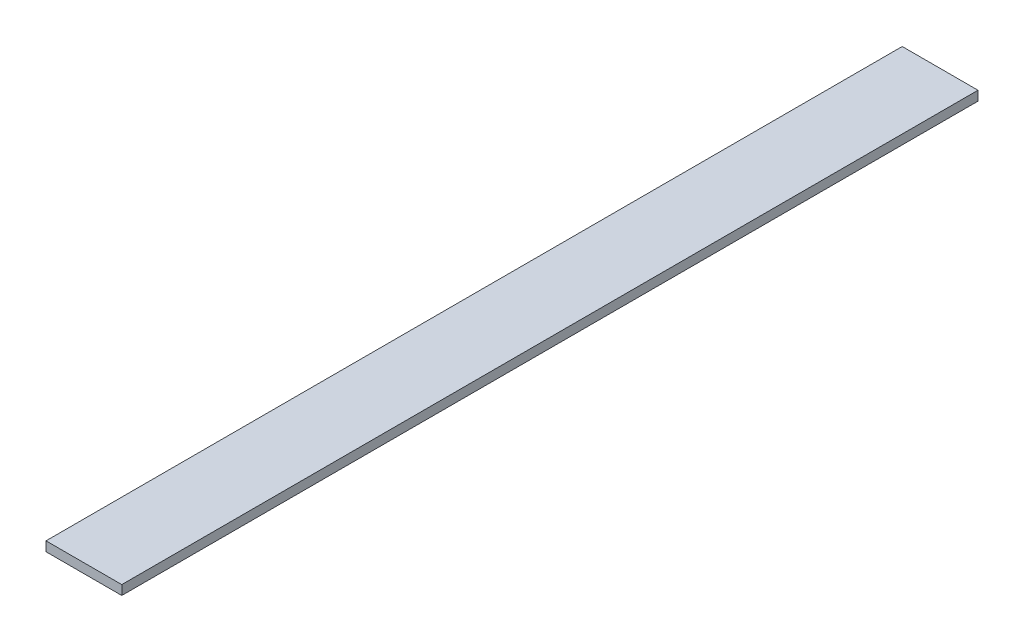
SolidWorks part; units mm, degrees
ref_plane "Спереди" through (0, 0, 0) normal (0, 0, 1) x (1, 0, 0)
ref_plane "Сверху" through (0, 0, 0) normal (0, 1, 0) x (1, 0, 0)
ref_plane "Справа" through (0, 0, 0) normal (1, 0, 0) x (0, 0, -1)
sketch "Эскиз1" plane through (0, 0, 0) normal (0, 0, 1) x (1, 0, 0)
  line L1 (0, 0) -> (40, 0)
  line L2 (0, 0) -> (0, -5)
  line L3 (0, -5) -> (40, -5)
  line L4 (40, 0) -> (40, -5)
  dimension "D1" = 5
  dimension "D2" = 40
extrude "Бобышка-Вытянуть1" add sketch "Эскиз1" along normal blind 452
